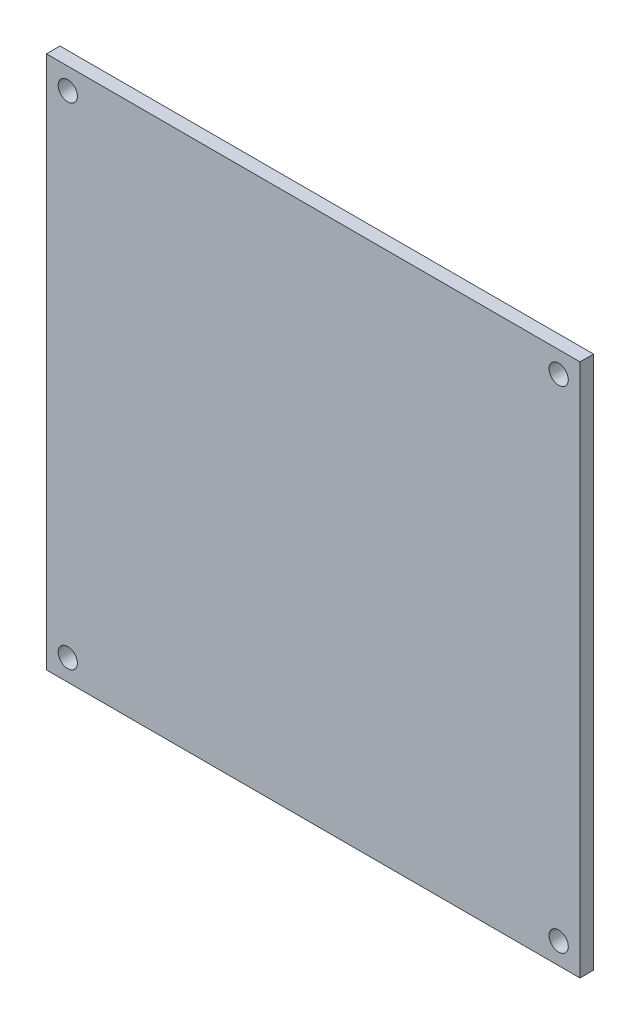
SolidWorks part; units mm, degrees
material "Acrylic (Medium-high impact)"
ref_plane "Plan de face" through (0, 0, 0) normal (0, 0, 1) x (1, 0, 0)
ref_plane "Plan de dessus" through (0, 0, 0) normal (0, 1, 0) x (1, 0, 0)
ref_plane "Plan de droite" through (0, 0, 0) normal (1, 0, 0) x (0, 0, -1)
sketch "Sketch1" plane through (0, 0, 0) normal (0, 0, 1) x (1, 0, 0)
  line L1 (62.5, -62.5) -> (-62.5, -62.5)
  line L2 (62.5, -62.5) -> (62.5, 62.5)
  line L3 (62.5, 62.5) -> (-62.5, 62.5)
  line L4 (-62.5, -62.5) -> (-62.5, 62.5)
  line L5 (62.5, -62.5) -> (-62.5, 62.5) construction
  line L6 (62.5, 62.5) -> (-62.5, -62.5) construction
  point P0 (0, 0)
  dimension "D1" = 125
  dimension "D2" = 125
extrude "Boss-Extrude1" add sketch "Sketch1" along normal blind 3.175
sketch "Sketch2" plane through (0, 0, 3.175) normal (0, 0, 1) x (1, 0, 0)
  line L0 (0, -62.5) -> (0, 62.5) construction
  line L1 (-62.5, -62.5) -> (62.5, -62.5) construction
  line L2 (62.5, 62.5) -> (-62.5, 62.5) construction
  line L3 (-62.5, 62.5) -> (-62.5, -62.5) construction
  circle A0 centre (-57.5, 57.5) radius 2.25
  circle A1 centre (-57.5, -57.5) radius 2.25
  circle A4 centre (57.5, -57.5) radius 2.25
  circle A5 centre (57.5, 57.5) radius 2.25
  dimension "D5" = 4.5
  dimension "D6" = 4.5
  dimension "D1" = 5
  dimension "D2" = 5
  dimension "D3" = 5
  dimension "D4" = 5
extrude "Cut-Extrude2" cut sketch "Sketch2" against normal blind 3.175
